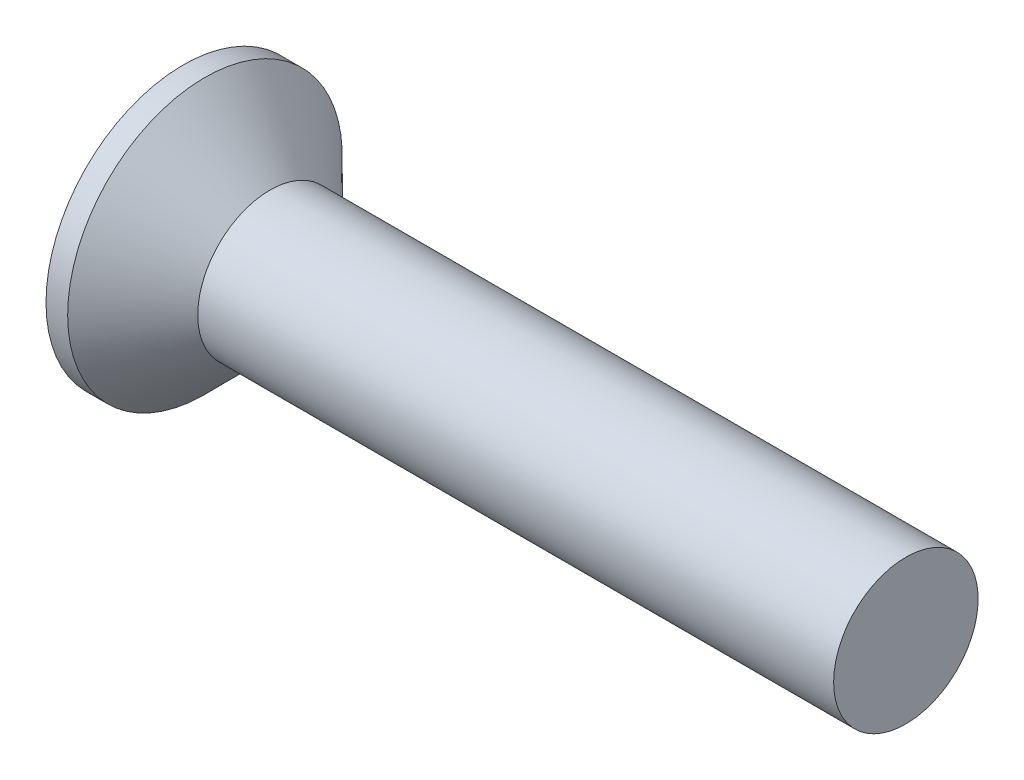
SolidWorks part; units mm, degrees
revolve "Base-Revolve" add sketch "BodySke" angle 360 about L5
sketch "BodySke" plane through (0, 0, 0) normal (0, 0, 1) x (1, 0, 0)
  line L0 (0, 0) -> (0, 1.9)
  line L1 (0, 1.9) -> (0.3, 1.9)
  line L2 (1.2, 1) -> (10, 1)
  line L3 (10, 1) -> (10, 0)
  line L4 (10, 0) -> (0, 0)
  line L5 (-6.35, 0) -> (82.55, 0) construction
  line L6 (1.2, -1) -> (10, -1) construction
  line L7 (0.3, -1.9) -> (1.2, -1) construction
  line L8 (0.3, 1.9) -> (1.2, 1)
  line L9 (0, -1.9) -> (0.3, -1.9) construction
  line L10 (1.6, 2.5875) -> (1.6, -6.9375) construction
  line L11 (0, 6.35) -> (0, -3.175) construction
  dimension "Diameter" = 2
  dimension "Length" = 10
  dimension "Head_ht" = 1.2
  dimension "Head_dia" = 3.8
  dimension "Head_ang" = 90
  dimension "D6" = 0.3
  dimension "Advance" = 0.4
  dimension "Thread_nom" = 10
cosmetic thread "ThreadCosmetic" parameters "Thread_length"=8.4, "Thread_minor"=1.548
extrude "Slot" [suppressed] cut sketch "Sketch2" against normal blind 0.6
sketch "Sketch2" plane through (0, 0, 0) normal (-1, 0, 0) x (0, 0, 1)
  line L0 (-1.9, -0.35) -> (1.9, -0.35)
  line L1 (-1.9, -0.35) -> (-1.9, 0.35)
  line L2 (1.9, 0.35) -> (-1.9, 0.35)
  line L3 (1.9, 0.35) -> (1.9, -0.35)
  dimension "Slot_width" = 0.7
  dimension "D1" = 0.35
  dimension "D2" = 3.8
  dimension "D3" = 1.9
ref_plane "Plane1" through (0, 0, 0) normal (0, 0, 1) x (1, 0, 0)
ref_plane "Plane2" through (0, 0, 0) normal (0, 1, 0) x (1, 0, 0)
ref_plane "Plane3" through (0, 0, 0) normal (1, 0, 0) x (0, 0, -1)
other "Configuration Table"
sketch "Sketch3" plane through (0, 0, 0) normal (-1, 0, 0) x (0, 0, 1)
  line L0 (-0.265, 1.07) -> (0.265, 1.07)
  line L1 (0.265, 1.07) -> (0.265, -1.07)
  line L2 (0.265, -1.07) -> (-0.265, -1.07)
  line L3 (-0.265, -1.07) -> (-0.265, 1.07)
  dimension "Cross_dia" = 2.14
  dimension "Cross_width" = 0.53
  dimension "D1" = 1.07
  dimension "D2" = 0.265
ref_plane "Plane4" through (1.54, 0, 0) normal (-1, 0, 0) x (0, 0, 1)
sketch "Sketch4" plane through (1.54, 0, 0) normal (-1, 0, 0) x (0, 0, 1)
  line L0 (-0.1325, 0.1325) -> (0.1325, 0.1325)
  line L3 (0.1325, 0.1325) -> (0.1325, -0.1325)
  line L4 (0.1325, -0.1325) -> (-0.1325, -0.1325)
  line L5 (-0.1325, -0.1325) -> (-0.1325, 0.1325)
  dimension "D2" = 0.265
  dimension "D1" = 0.265
  dimension "D3" = 0.1325
  dimension "D4" = 0.1325
loft "Cross" cut profiles "Sketch3", "Sketch4"
pattern_circular "CirPattern1" count 2 every 90 about axis through (0, 0, 0) along (1, 0, 0) of "Cross"
sketch "ThdSchSke" plane through (0, 0, 0) normal (0, 0, 1) x (1, 0, 0)
  line L0 (1.6, -0.774) -> (1.4418, -1)
  line L1 (1.6, -0.774) -> (1.7582, -1)
  line L2 (1.7582, -1) -> (1.7582, -1.25)
  line L3 (-3.175, 0) -> (5.1513, 0) construction
  line L5 (1.7582, -1.25) -> (1.4418, -1.25)
  line L6 (1.4418, -1.25) -> (1.4418, -1)
  line L7 (0, 1.9) -> (0, -1.9) construction
  dimension "Diameter" = 2
  dimension "Thread_minor" = 1.548
  dimension "Start" = 1.6
revolve "ThreadSchematic" [suppressed] cut sketch "ThdSchSke" angle 360 about L3
pattern_linear "ThdSchPat" [suppressed]
equation "\"D1@Sketch3\" = \"Cross_dia@Sketch3\" / 2"
equation "\"D2@Sketch3\" = \"Cross_width@Sketch3\" / 2"
equation "\"D1@Sketch4\" = \"Cross_width@Sketch3\" *.5"
equation "\"D2@Sketch4\" = \"D1@Sketch4\""
equation "\"D4@Sketch4\" = \"D2@Sketch4\" / 2"
equation "\"D3@Sketch4\" = \"D1@Sketch4\" / 2"
equation "\"D1@Sketch2\" = \"Slot_width@Sketch2\" / 2"
equation "\"D2@Sketch2\" = \"Head_dia@BodySke\""
equation "\"D3@Sketch2\" = \"D2@Sketch2\" / 2"
equation "\"Thread_length@ThreadCosmetic\" = ((sgn( (\"Length@BodySke\" - \"Advance@BodySke\" - \"Head_ht@BodySke\" ) - \"Thread_nom@BodySke\" )-1)*( (\"Length@BodySke\" - \"Advance@BodySke\" - \"Head_ht@BodySke\" ) - \"Thread_nom@BodySke\" ))/-2+ \"Thread_nom@BodySke\""
equation "\"Thread_minor@ThdSchSke\" = \"Thread_minor@ThreadCosmetic\""
equation "\"Diameter@ThdSchSke\" = \"Diameter@BodySke\""
equation "\"Overcut@ThdSchSke\" = \"Diameter@BodySke\" * 1.25"
equation "\"Start@ThdSchSke\" = 0.000001 + \"Length@BodySke\" - \"Thread_length@ThreadCosmetic\"  '---Countersunk---"
equation "\"Num_threads@ThdSchPat\" = int( \"Thread_length@ThreadCosmetic\" / \"Advance@BodySke\" + 0.999 )  + 1"
equation "\"Advance@ThdSchPat\" = \"Thread_length@ThreadCosmetic\" /  (\"Num_threads@ThdSchPat\" - 1) 'relax it"
